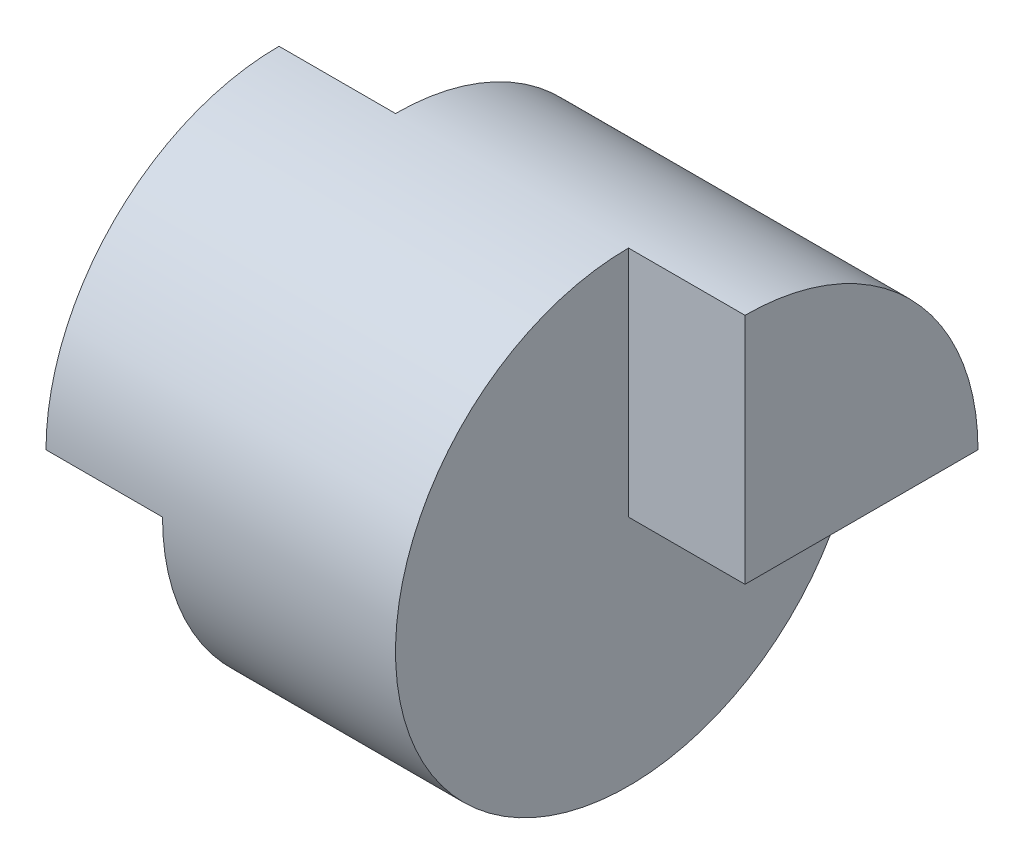
SolidWorks part; units mm, degrees
ref_plane "Front Plane" through (0, 0, 0) normal (0, 0, 1) x (1, 0, 0)
ref_plane "Top Plane" through (0, 0, 0) normal (0, 1, 0) x (1, 0, 0)
ref_plane "Right Plane" through (0, 0, 0) normal (1, 0, 0) x (0, 0, -1)
sketch "Sketch5" plane through (0, 0, 0) normal (0, 0, 1) x (1, 0, 0)
  line L0 (0, 0) -> (4, 0)
  dimension "D1" = 4
revolve "Revolve-Thin2" add sketch "Sketch5" angle 360 about L0 wall 2
sketch "Sketch6" plane through (0, 0, 0) normal (0, 0, 1) x (1, 0, 0)
  line L1 (1, 0) -> (0, 0)
  line L2 (1, 0) -> (1, -2)
  line L3 (1, -2) -> (0, -2)
  line L4 (0, 0) -> (0, -2)
  line L5 (4, -2) -> (3, -2)
  line L6 (4, -2) -> (4, 0)
  line L7 (4, 0) -> (3, 0)
  line L8 (3, -2) -> (3, 0)
  dimension "D1" = 1
  dimension "D2" = 1
  dimension "D3" = 2
  dimension "D4" = 2
extrude "Cut-Extrude5" cut sketch "Sketch6" against normal mid plane 11 contours L5 L8 L7 L6 | L4 L1 L2 L3 | L1 L4 L3 L2 | L8 L5 L6 L7
sketch "Sketch7" plane through (0, 0, 0) normal (0, -1, 0) x (1, 0, 0)
  line L0 (4, 2) -> (3, 2) construction
  line L1 (0, -2) -> (2, -2)
  line L2 (0, -2) -> (0, 0)
  line L3 (0, 0) -> (2, 0)
  line L4 (2, -2) -> (2, 0)
  line L7 (4, 0) -> (3, 0)
  line L9 (3, 0) -> (4, 0)
  line L10 (3, 0) -> (3, 2)
  line L11 (3, 2) -> (4, 2)
  line L12 (4, 0) -> (4, 2)
  line L13 (4, -2) -> (4, 2) construction
  line M5 (0, -2) -> (1, -2)
  line M6 (1, -2) -> (1, 2)
  line M8 (0, 2) -> (0, -2)
  dimension "D2" = 2
  dimension "D3" = 2
  dimension "D4" = 1
extrude "Cut-Extrude6" cut sketch "Sketch7" against normal blind 10 contours L3 M8 M5 M6 | L7 L12 L11 L10
